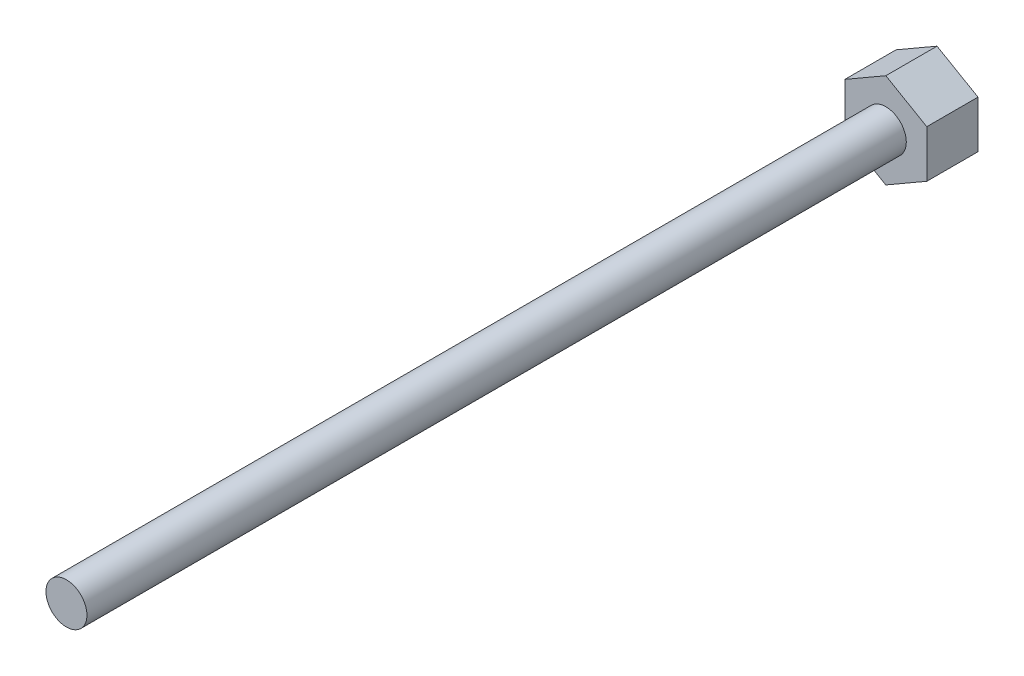
SolidWorks part; units mm, degrees
material "201 Annealed Stainless Steel (SS)"
ref_plane "Front Plane" through (0, 0, 0) normal (0, 0, 1) x (1, 0, 0)
ref_plane "Top Plane" through (0, 0, 0) normal (0, 1, 0) x (1, 0, 0)
ref_plane "Right Plane" through (0, 0, 0) normal (1, 0, 0) x (0, 0, -1)
sketch "Sketch1" plane through (0, 0, 0) normal (0, 0, 1) x (1, 0, 0)
  circle A0 centre (0, 0) radius 2
  dimension "D1" = 4
extrude "Boss-Extrude1" add sketch "Sketch1" along normal blind 80
sketch "Sketch2" plane through (0, 0, 0) normal (0, 0, -1) x (-1, 0, 0)
  line L1 (0, 4.6188) -> (-4, 2.3094)
  line L2 (-4, 2.3094) -> (-4, -2.3094)
  line L3 (-4, -2.3094) -> (0, -4.6188)
  line L4 (0, -4.6188) -> (4, -2.3094)
  line L5 (4, -2.3094) -> (4, 2.3094)
  line L6 (4, 2.3094) -> (0, 4.6188)
  circle A0 centre (0, 0) radius 4 construction
  dimension "D1" = 8
extrude "Boss-Extrude2" add sketch "Sketch2" along normal blind 5
